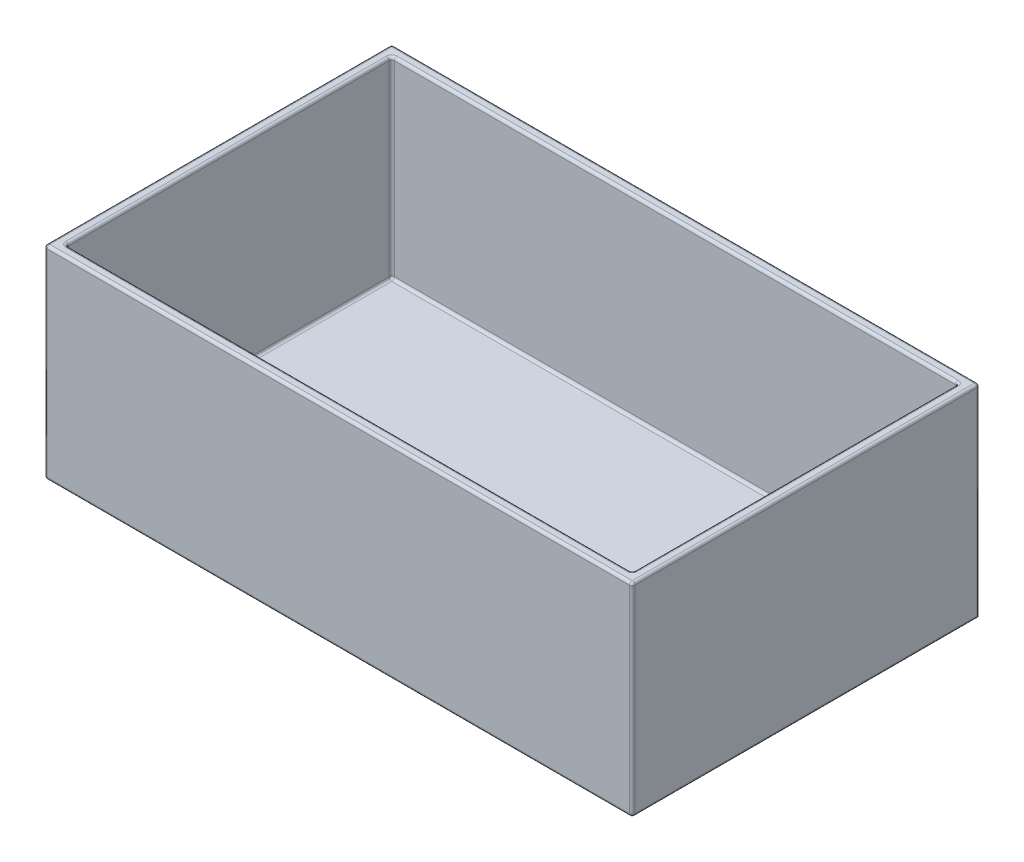
SolidWorks part; units mm, degrees
ref_plane "Front Plane" through (0, 0, 0) normal (0, 0, 1) x (1, 0, 0)
ref_plane "Top Plane" through (0, 0, 0) normal (0, 1, 0) x (1, 0, 0)
ref_plane "Right Plane" through (0, 0, 0) normal (1, 0, 0) x (0, 0, -1)
sketch "Sketch1" plane through (0, 0, 0) normal (0, 1, 0) x (1, 0, 0)
  line L1 (-43.0882, 37.0588) -> (66.9118, 37.0588)
  line L2 (-43.0882, 37.0588) -> (-43.0882, -27.9412)
  line L3 (-43.0882, -27.9412) -> (66.9118, -27.9412)
  line L4 (66.9118, 37.0588) -> (66.9118, -27.9412)
  dimension "D1" = 110
  dimension "D2" = 65
extrude "Boss-Extrude1" add sketch "Sketch1" along normal blind 38 contours L3 L4 L1 L2
sketch "Sketch2" plane through (0, 38, 0) normal (0, 1, 0) x (1, 0, 0)
  line L0 (-43.0882, 37.0588) -> (-43.0882, -27.9412) construction
  line L1 (-41.0882, 35.0588) -> (64.9118, 35.0588)
  line L2 (-41.0882, 35.0588) -> (-41.0882, -25.9412)
  line L3 (-41.0882, -25.9412) -> (64.9118, -25.9412)
  line L4 (64.9118, 35.0588) -> (64.9118, -25.9412)
  line L5 (-43.0882, -27.9412) -> (66.9118, -27.9412) construction
  line L6 (66.9118, 37.0588) -> (66.9118, -27.9412) construction
  line L7 (-43.0882, 37.0588) -> (66.9118, 37.0588) construction
  point P6 (-41.0882, 4.5588)
  dimension "D1" = 2
  dimension "D2" = 2
  dimension "D3" = 2
  dimension "D4" = 2
extrude "Cut-Extrude1" cut sketch "Sketch2" against normal blind 36
sketch "Sketch3" plane through (0, 2, 0) normal (0, 1, 0) x (1, 0, 0)
  line L0 (64.9118, 35.0588) -> (-41.0882, 35.0588) construction
  line L1 (36.9118, 35.0588) -> (38.9118, 35.0588)
  line L2 (36.9118, 35.0588) -> (36.9118, -25.9412)
  line L3 (36.9118, -25.9412) -> (38.9118, -25.9412)
  line L4 (38.9118, 35.0588) -> (38.9118, -25.9412)
  line L5 (-41.0882, -25.9412) -> (64.9118, -25.9412) construction
  line L6 (64.9118, -25.9412) -> (64.9118, 35.0588) construction
  dimension "D2" = 2
  dimension "D1" = 26
extrude "Boss-Extrude2" add sketch "Sketch3" along normal blind 5 contours L4 L3 L2 L1
fillet "Fillet4" radius 0.5 35 edges at (38.9118, 4.5, 25.9412) (-43.0882, 19, -37.0588) (-43.0882, 0, -4.5588) (64.9118, 20, 25.9412) (36.9118, 4.5, 25.9412) (38.9118, 7, -4.5588) (37.9118, 7, 25.9412) (36.9118, 7, -4.5588) (64.9118, 2, -4.5588) (51.9118, 2, 25.9412) (38.9118, 2, -4.5588) (-41.0882, 20, 25.9412) (-41.0882, 2, -4.5588) (36.9118, 2, -4.5588) (-2.0882, 2, 25.9412) (-2.0882, 2, -35.0588) (-41.0882, 20, -35.0588) (64.9118, 20, -35.0588) (51.9118, 2, -35.0588) (38.9118, 4.5, -35.0588) (37.9118, 7, -35.0588) (36.9118, 4.5, -35.0588) (66.9118, 19, -37.0588) (66.9118, 0, -4.5588) (-43.0882, 19, 27.9412) (66.9118, 19, 27.9412) (11.9118, 0, 27.9412) (11.9118, 38, -37.0588) (66.9118, 38, -4.5588) (11.9118, 38, 27.9412) (-43.0882, 38, -4.5588) (11.9118, 38, 25.9412) (64.9118, 38, -4.5588) (11.9118, 38, -35.0588) (-41.0882, 38, -4.5588)
equation "\"boxlengthout\"=180"
equation "\"boxwidthout\"= 120"
equation "\"D1@Sketch1\"=\"boxthickenss\"*3+\"batterywidth\"+\"boardlength\"+2"
equation "\"board_arduinoheight\"= 24"
equation "\"boardwidth\"= 60"
equation "\"boardlength\"= 77"
equation "\"batterylength\"= 48"
equation "\"batterywidth\"= 25"
equation "\"batteryheight\"= 15"
equation "\"boxthickenss\"= 2"
equation "\"D2@Sketch1\"=\"boardwidth\"+\"boxthickenss\"*2+1"
equation "\"D1@Boss-Extrude1\"=\"board_arduinoheight\"+\"boxthickenss\"*2+10"
equation "\"D1@Sketch2\"=\"boxthickenss\""
equation "\"D2@Sketch2\"=\"boxthickenss\""
equation "\"D3@Sketch2\"=\"boxthickenss\""
equation "\"D4@Sketch2\"=\"boxthickenss\""
equation "\"D1@Cut-Extrude1\"=\"board_arduinoheight\"+\"boxthickenss\"+10"
equation "\"D1@Sketch3\"=\"batterywidth\"+1"
equation "\"D2@Sketch3\"=\"boxthickenss\""
equation "\"dividerheight\"=5"
equation "\"D1@Boss-Extrude2\"=\"dividerheight\""
